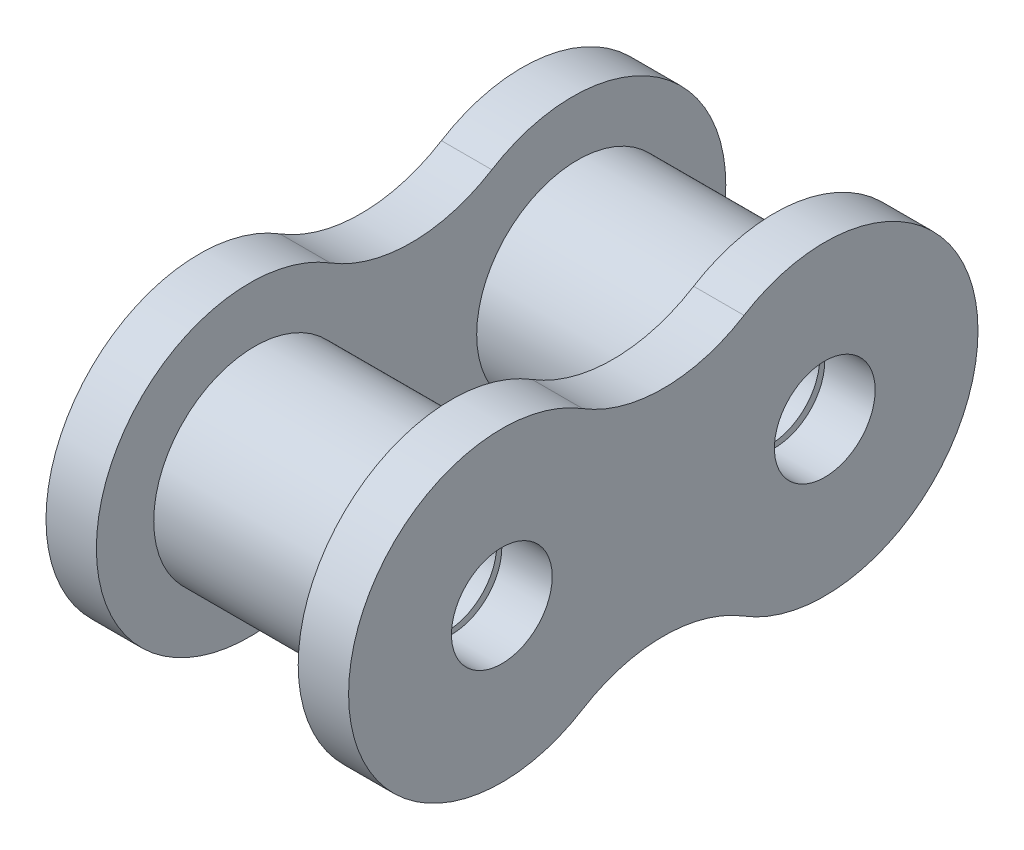
SolidWorks part; units mm, degrees
material "Alloy Steel"
ref_plane "Front" through (0, 0, 0) normal (0, 0, 1) x (1, 0, 0)
ref_plane "Top" through (0, 0, 0) normal (0, 1, 0) x (1, 0, 0)
ref_plane "Right" through (0, 0, 0) normal (1, 0, 0) x (0, 0, -1)
ref_plane "Back Link Plane" through (-7.9375, 0, 0) normal (1, 0, 0) x (0, 0, -1)
ref_plane "Front Link Plane" through (7.9375, 0, 0) normal (1, 0, 0) x (0, 0, -1)
ref_plane "F/F Pin Plane" through (0, 0, 12.7) normal (0, 0, 1) x (1, 0, 0)
ref_plane "F/B Pin Plane" through (0, 0, -12.7) normal (0, 0, 1) x (1, 0, 0)
sketch "Back Link Sketch" plane through (-7.9375, 0, 0) normal (1, 0, 0) x (0, 0, -1)
  line L0 (0, -33.7816) -> (0, 28.0067) construction
  line L1 (59.1569, 0) -> (-51.6942, 0) construction
  arc A0 (-6.35, 10.2438) -> (-6.35, -10.2438) centre (-12.7, 0) ccw
  arc A1 (-6.35, -10.2438) -> (6.35, -10.2438) centre (0, -20.4876) cw
  arc A2 (6.35, -10.2438) -> (6.35, 10.2438) centre (12.7, 0) ccw
  arc A3 (6.35, 10.2438) -> (-6.35, 10.2438) centre (0, 20.4876) cw
  circle A4 centre (-12.7, 0) radius 3.9624
  circle A5 centre (12.7, 0) radius 3.9624
  dimension "D" = 7.9248
  dimension "Ho" = 24.1046
  dimension "Ho-1" = 12.0523
  dimension "P" = 25.4
  dimension "P-1" = 12.7
  dimension "Ho-2" = 24.1046
  dimension "Ho-3" = 24.1046
extrude "Back Link Extrude" add sketch "Back Link Sketch" against normal blind 3.9624
sketch "Front Link Sketch" plane through (7.9375, 0, 0) normal (1, 0, 0) x (0, 0, -1)
  circle A0 centre (-12.7, 0) radius 3.9624 construction
  circle A1 centre (12.7, 0) radius 3.9624 construction
  circle A2 centre (-12.7, 0) radius 3.9624
  circle A3 centre (12.7, 0) radius 3.9624
  arc A4 (-6.35, 10.2438) -> (6.35, 10.2438) centre (0, 20.4876) ccw
  arc A5 (-6.35, 10.2438) -> (-6.35, -10.2438) centre (-12.7, 0) ccw
  arc A6 (6.35, -10.2438) -> (-6.35, -10.2438) centre (0, -20.4876) ccw
  arc A7 (6.35, -10.2438) -> (6.35, 10.2438) centre (12.7, 0) ccw
  arc A8 (-6.35, 10.2438) -> (6.35, 10.2438) centre (0, 20.4876) ccw
  arc A9 (-6.35, 10.2438) -> (-6.35, -10.2438) centre (-12.7, 0) ccw
  arc A10 (6.35, -10.2438) -> (-6.35, -10.2438) centre (0, -20.4876) ccw
  arc A11 (6.35, -10.2438) -> (6.35, 10.2438) centre (12.7, 0) ccw
  dimension "D1" = 0
extrude "Front Link Extrude" add sketch "Front Link Sketch" along normal blind 3.9624
sketch "Roller Sketch" plane through (0, 0, 0) normal (1, 0, 0) x (0, 0, -1)
  circle A0 centre (12.7, 0) radius 3.9624 construction
  circle A1 centre (-12.7, 0) radius 3.9624 construction
  circle A2 centre (12.7, 0) radius 3.9624
  circle A3 centre (-12.7, 0) radius 3.9624
  circle A4 centre (12.7, 0) radius 7.9375
  circle A5 centre (-12.7, 0) radius 7.9375
  dimension "R" = 15.875
extrude "Roller Extrude" add sketch "Roller Sketch" along normal blind 7.5406 and the other way blind 7.5406
ref_point "Pin Point 1"
ref_point "Pin Point 2"
equation "\"D1@F/F Pin Plane\" = \"P@Back Link Sketch\" * 0.50"
equation "\"D1@F/B Pin Plane\" = \"P@Back Link Sketch\" * 0.50"
equation "\"Ho-1@Back Link Sketch\" = \"Ho@Back Link Sketch\" * 0.50"
equation "\"Ho-2@Back Link Sketch\" = \"Ho@Back Link Sketch\""
equation "\"Ho-3@Back Link Sketch\" = \"Ho@Back Link Sketch\""
equation "\"P-1@Back Link Sketch\" = \"P@Back Link Sketch\" * 0.50"
equation "\"D1@Front Link Plane\" = \"D1@Back Link Plane\""
equation "\"D1@Front Link Extrude\" = \"D1@Back Link Extrude\""
equation "\"D2@Roller Extrude\" = \"D1@Roller Extrude\""
